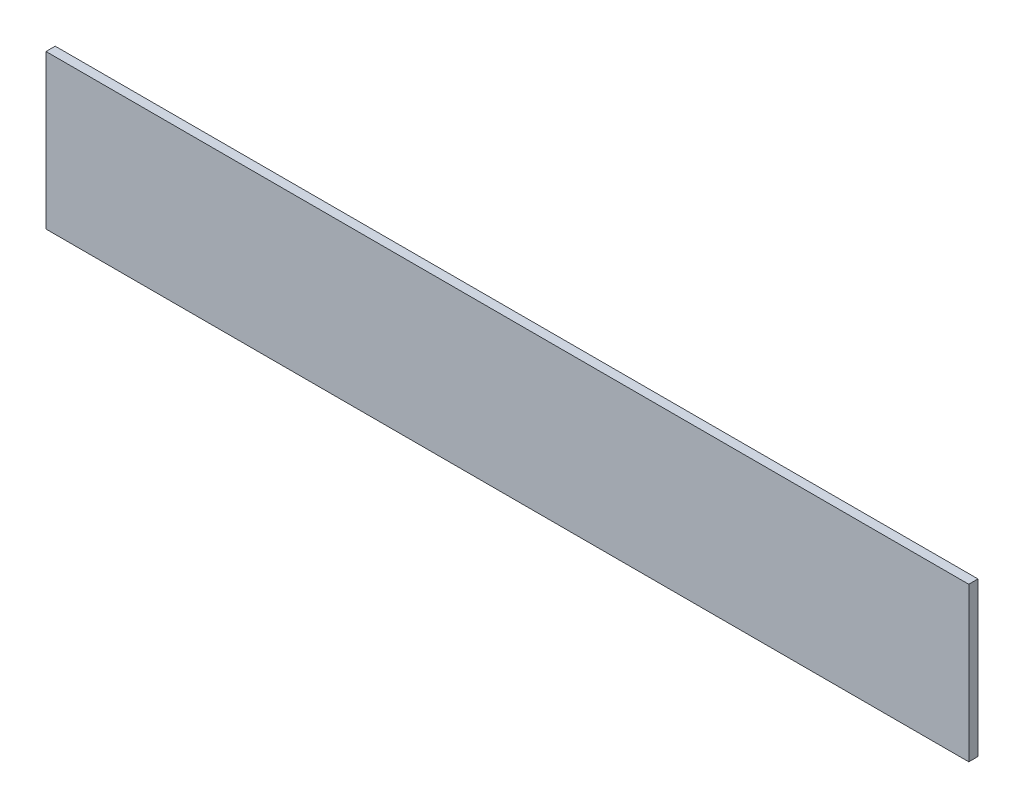
SolidWorks part; units mm, degrees
ref_plane "Front Plane" through (0, 0, 0) normal (0, 0, 1) x (1, 0, 0)
ref_plane "Top Plane" through (0, 0, 0) normal (0, 1, 0) x (1, 0, 0)
ref_plane "Right Plane" through (0, 0, 0) normal (1, 0, 0) x (0, 0, -1)
sketch "Sketch1" plane through (0, 0, 0) normal (0, 0, 1) x (1, 0, 0)
  line L1 (-150, -25) -> (150, -25)
  line L2 (-150, -25) -> (-150, 25)
  line L3 (-150, 25) -> (150, 25)
  line L4 (150, -25) -> (150, 25)
  line L5 (-150, -25) -> (150, 25) construction
  line L6 (-150, 25) -> (150, -25) construction
  point P0 (0, 0)
  dimension "D1" = 50
  dimension "D2" = 300
extrude "Boss-Extrude1" add sketch "Sketch1" along normal blind 3
